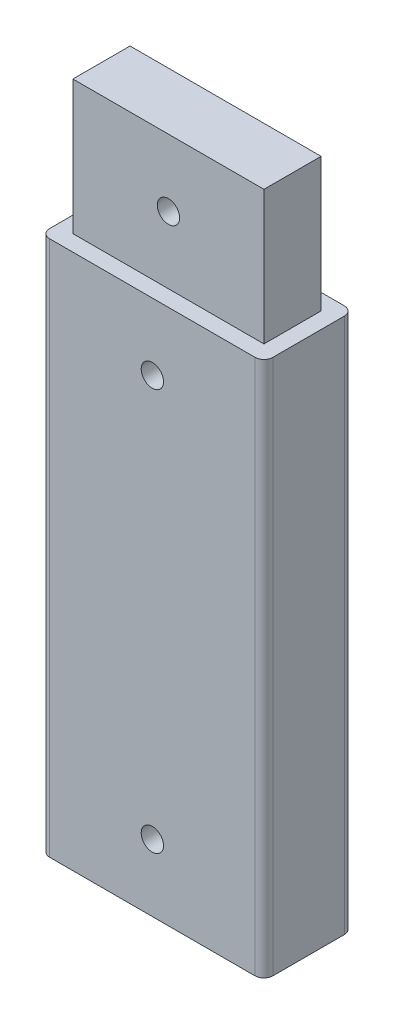
SolidWorks part; units mm, degrees
ref_plane "Front Plane" through (0, 0, 0) normal (0, 0, 1) x (1, 0, 0)
ref_plane "Top Plane" through (0, 0, 0) normal (0, 1, 0) x (1, 0, 0)
ref_plane "Right Plane" through (0, 0, 0) normal (1, 0, 0) x (0, 0, -1)
sketch "Sketch1" plane through (0, 0, 0) normal (0, 1, 0) x (1, 0, 0)
  line L1 (2, 0) -> (48, 0)
  line L2 (0, 2) -> (0, 18)
  line L3 (2, 20) -> (48, 20)
  line L4 (50, 2) -> (50, 18)
  arc A0 (2, 0) -> (0, 2) centre (2, 2) cw
  arc A1 (48, 0) -> (50, 2) centre (48, 2) ccw
  arc A2 (48, 20) -> (50, 18) centre (48, 18) cw
  arc A3 (0, 18) -> (2, 20) centre (2, 18) cw
  point P7 (0, 0)
  point P12 (50, 20)
  point P15 (0, 20)
  dimension "D3" = 2
  dimension "D1" = 50
  dimension "D2" = 20
extrude "Boss-Extrude1" add sketch "Sketch1" along normal blind 120
sketch "Sketch3" plane through (0, 0, 0) normal (0, -1, 0) x (1, 0, 0)
  line L29 (46, -16) -> (46, -4)
  line L30 (4, -16) -> (46, -16)
  line L31 (4, -4) -> (4, -16)
  line L32 (46, -4) -> (4, -4)
  line L33 (46, -16) -> (46, -4)
  line L34 (4, -16) -> (46, -16)
  line L35 (4, -4) -> (4, -16)
  line L36 (46, -4) -> (4, -4)
  dimension "D1" = 4
extrude "Cut-Extrude2" cut sketch "Sketch3" against normal blind 30 contours L35 L34 L33 L36
sketch "Sketch6" plane through (0, 0, 0) normal (0, 0, 1) x (1, 0, 0)
  line L0 (50, 120) -> (50, 0) construction
  line L1 (2, 120) -> (48, 120) construction
  line L2 (2, 0) -> (48, 0) construction
  circle A0 centre (25, 105) radius 2.5
  circle A1 centre (25, 15) radius 2.5
  dimension "D1" = 25
  dimension "D3" = 15
  dimension "D2" = 15
extrude "Cut-Extrude3" cut sketch "Sketch6" against normal blind 30
sketch "Sketch8" plane through (0, 120, 0) normal (0, 1, 0) x (1, 0, 0)
  line L20 (3.6, 16.4) -> (3.6, 3.6)
  line L21 (3.6, 3.6) -> (46.4, 3.6)
  line L22 (46.4, 3.6) -> (46.4, 16.4)
  line L23 (46.4, 16.4) -> (3.6, 16.4)
  line L24 (3.6, 16.4) -> (3.6, 3.6)
  line L25 (3.6, 3.6) -> (46.4, 3.6)
  line L26 (46.4, 3.6) -> (46.4, 16.4)
  line L27 (46.4, 16.4) -> (3.6, 16.4)
  dimension "D1" = 3.6
extrude "Boss-Extrude2" add sketch "Sketch8" along normal blind 30
sketch "Sketch9" plane through (0, 0, -3.6) normal (0, 0, 1) x (1, 0, 0)
  line L0 (46.4, 150) -> (46.4, 120) construction
  line L1 (3.6, 150) -> (46.4, 150) construction
  circle A0 centre (25, 135) radius 2.5
  point P4 (0, 0)
  dimension "D1" = 21.4
  dimension "D2" = 15
extrude "Cut-Extrude4" cut sketch "Sketch9" against normal blind 30
